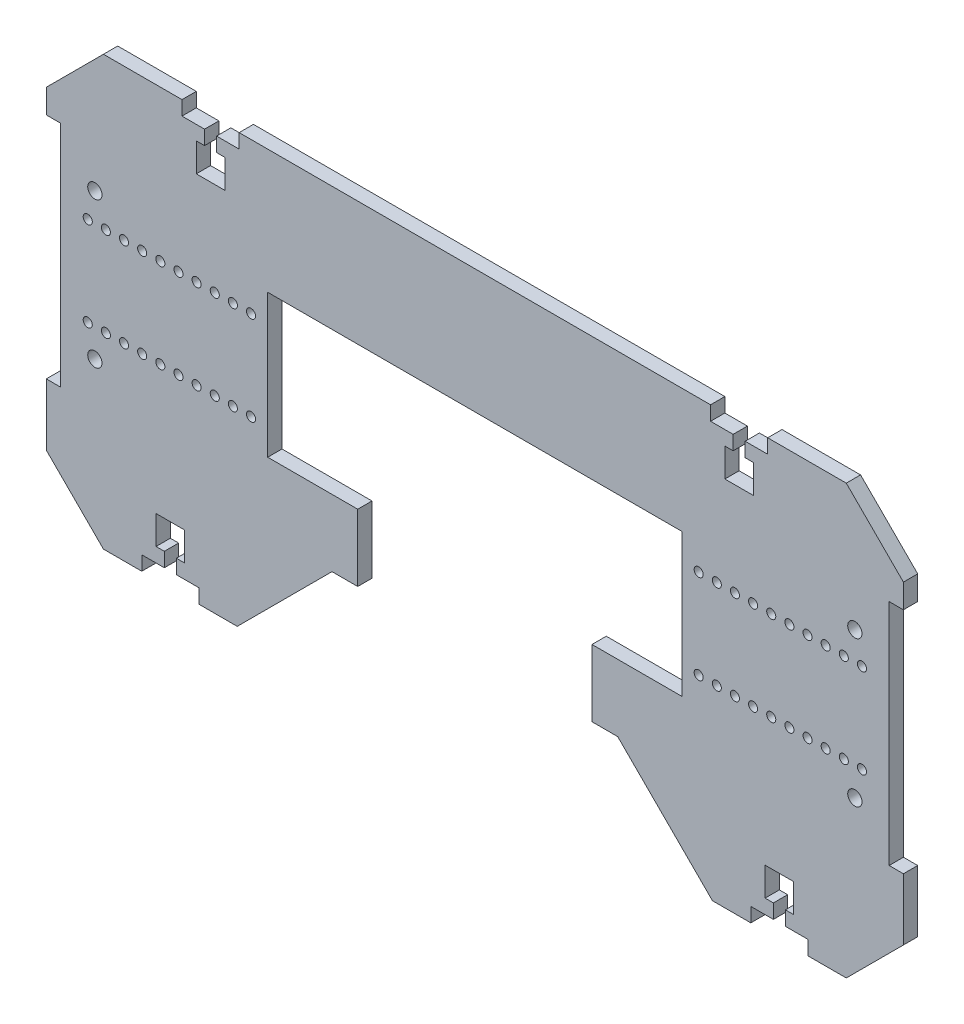
SolidWorks part; units mm, degrees
ref_plane "Front Plane" through (0, 0, 0) normal (0, 0, 1) x (1, 0, 0)
ref_plane "Top Plane" through (0, 0, 0) normal (0, 1, 0) x (1, 0, 0)
ref_plane "Right Plane" through (0, 0, 0) normal (1, 0, 0) x (0, 0, -1)
sketch "Sketch1" plane through (0, 0, 0) normal (0, 0, 1) x (1, 0, 0)
  line L3 (-32.7679, -18.8009) -> (-32.7679, 31.1991)
  line L4 (-72.7679, 31.1991) -> (-32.7679, 31.1991)
  line L5 (-32.7679, -18.8009) -> (-72.7679, -18.8009)
  line L6 (149.7321, -33.8009) -> (144.7321, -33.8009)
  line L7 (144.7321, -33.8009) -> (144.7321, 46.1991)
  line L8 (144.7321, 46.1991) -> (149.7321, 46.1991)
  line L9 (149.7321, 46.1991) -> (149.7321, 54.5982)
  line L10 (149.7321, 54.5982) -> (129.7321, 74.5982)
  line L11 (129.7321, 74.5982) -> (-130.2679, 74.5982)
  line L12 (-130.2679, 74.5982) -> (-150.2679, 54.5982)
  line L13 (-150.2679, 54.5982) -> (-150.2679, 46.1991)
  line L14 (-150.2679, 46.1991) -> (-145.2679, 46.1991)
  line L15 (-145.2679, 46.1991) -> (-145.2679, -33.8009)
  line L16 (-145.2679, -33.8009) -> (-150.2679, -33.8009)
  line L17 (-150.2679, -33.8009) -> (-150.2679, -55.4018)
  line L18 (-150.2679, -55.4018) -> (-130.2679, -75.4018)
  line L19 (-130.2679, -75.4018) -> (-83.4341, -75.4018)
  line L20 (-83.4341, -75.4018) -> (-50.2679, -42.2355)
  line L21 (-50.2679, -42.2355) -> (-28.2679, -42.2355)
  line L22 (49.7321, -42.2355) -> (82.8984, -75.4018)
  line L23 (82.8984, -75.4018) -> (129.7321, -75.4018)
  line L24 (129.7321, -75.4018) -> (149.7321, -55.4018)
  line L25 (149.7321, -55.4018) -> (149.7321, -33.8009)
  line L40 (27.7321, -42.2355) -> (49.7321, -42.2355)
  line L41 (-72.7679, 31.1991) -> (-72.7679, -18.8009)
  line L44 (-25.2679, -39.2355) -> (-25.2679, 1.2645)
  line L45 (-22.2679, 4.2645) -> (21.7321, 4.2645)
  line L46 (24.7321, -39.2355) -> (24.7321, 1.2645)
  line L47 (-32.7679, 31.1991) -> (-72.7679, -18.8009) construction
  line L48 (-52.7679, 6.1991) -> (-52.7679, 74.5982) construction
  line L49 (-52.7679, 6.1991) -> (-145.2679, 6.1991) construction
  line L50 (-0.2679, 74.5982) -> (-0.2679, 51.6893) construction
  line L51 (32.2321, -18.8009) -> (72.2321, -18.8009)
  line L52 (32.2321, -18.8009) -> (32.2321, 31.1991)
  line L53 (72.2321, 31.1991) -> (32.2321, 31.1991)
  line L54 (72.2321, 31.1991) -> (72.2321, -18.8009)
  arc A8 (24.7321, -39.2355) -> (27.7321, -42.2355) centre (27.7321, -39.2355) ccw
  arc A9 (-25.2679, -39.2355) -> (-28.2679, -42.2355) centre (-28.2679, -39.2355) cw
  arc A10 (21.7321, 4.2645) -> (24.7321, 1.2645) centre (21.7321, 1.2645) cw
  arc A11 (-25.2679, 1.2645) -> (-22.2679, 4.2645) centre (-22.2679, 1.2645) cw
  point P36 (24.7321, 4.2645)
  point P41 (-25.2679, 4.2645)
  point P56 (-0.2679, -20.7355)
  dimension "D22" = 3
  dimension "D1" = 260
  dimension "D2" = 28.2843
  dimension "D3" = 8.3991
  dimension "D4" = 80
  dimension "D5" = 21.6009
  dimension "D6" = 5
  dimension "D7" = 28.2843
  dimension "D8" = 46.8338
  dimension "D9" = 46.9042
  dimension "D10" = 46.9042
  dimension "D11" = 46.8338
  dimension "D12" = 28.2843
  dimension "D13" = 21.6009
  dimension "D14" = 80
  dimension "D15" = 8.3991
  dimension "D16" = 28.2843
  dimension "D17" = 40
  dimension "D18" = 50
  dimension "D21" = 50
extrude "Boss-Extrude1" add sketch "Sketch1" along normal blind 5
sketch "Sketch2" plane through (0, 0, 5) normal (0, 0, 1) x (1, 0, 0)
  line L0 (24.7321, 1.2645) -> (24.7321, -39.2355) construction
  line L1 (-25.2679, -39.2355) -> (-25.2679, 1.2645) construction
  line L2 (-22.2679, 4.2645) -> (21.7321, 4.2645) construction
  line L3 (24.7321, 1.2645) -> (24.7321, -39.2355)
  line L4 (-25.2679, -39.2355) -> (-25.2679, 1.2645)
  line L5 (-22.2679, 4.2645) -> (21.7321, 4.2645)
  line L6 (-29.2679, -38.3625) -> (-29.2679, 1.2645)
  line L7 (-22.2679, 8.2645) -> (21.7321, 8.2645)
  line L8 (28.7321, 1.2645) -> (28.7321, -38.3625)
  line L9 (-29.2679, -38.3625) -> (-29.2679, -42.2355)
  line L10 (-50.2679, -42.2355) -> (-28.2679, -42.2355) construction
  line L11 (28.7321, -38.3625) -> (28.7321, -42.2355)
  line L12 (27.7321, -42.2355) -> (49.7321, -42.2355) construction
  line L13 (27.7321, -42.2355) -> (28.7321, -42.2355)
  line L14 (-28.2679, -42.2355) -> (-29.2679, -42.2355)
  arc A0 (24.7321, -39.2355) -> (27.7321, -42.2355) centre (27.7321, -39.2355) ccw construction
  arc A1 (24.7321, 1.2645) -> (21.7321, 4.2645) centre (21.7321, 1.2645) ccw construction
  arc A2 (-28.2679, -42.2355) -> (-25.2679, -39.2355) centre (-28.2679, -39.2355) ccw construction
  arc A3 (-22.2679, 4.2645) -> (-25.2679, 1.2645) centre (-22.2679, 1.2645) ccw construction
  arc A4 (24.7321, -39.2355) -> (27.7321, -42.2355) centre (27.7321, -39.2355) ccw
  arc A5 (24.7321, 1.2645) -> (21.7321, 4.2645) centre (21.7321, 1.2645) ccw
  arc A6 (-28.2679, -42.2355) -> (-25.2679, -39.2355) centre (-28.2679, -39.2355) ccw
  arc A7 (-22.2679, 4.2645) -> (-25.2679, 1.2645) centre (-22.2679, 1.2645) ccw
  arc A8 (-29.2679, -38.3625) -> (-29.2679, -38.3625) centre (-29.2679, -38.3625) ccw
  arc A9 (-22.2679, 8.2645) -> (-29.2679, 1.2645) centre (-22.2679, 1.2645) ccw
  arc A10 (28.7321, 1.2645) -> (21.7321, 8.2645) centre (21.7321, 1.2645) ccw
  arc A11 (28.7321, -38.3625) -> (28.7321, -38.3625) centre (28.7321, -38.3625) ccw
  line M22 (-50.2679, -42.2355) -> (-28.2679, -42.2355)
  arc M23 (-28.2679, -42.2355) -> (-25.2679, -39.2355) centre (-28.2679, -39.2355) ccw
  line M24 (-25.2679, -39.2355) -> (-25.2679, 1.2645)
  arc M25 (-25.2679, 1.2645) -> (-22.2679, 4.2645) centre (-22.2679, 1.2645) cw
  line M26 (-22.2679, 4.2645) -> (21.7321, 4.2645)
  arc M27 (21.7321, 4.2645) -> (24.7321, 1.2645) centre (21.7321, 1.2645) cw
  line M28 (24.7321, 1.2645) -> (24.7321, -39.2355)
  arc M29 (24.7321, -39.2355) -> (27.7321, -42.2355) centre (27.7321, -39.2355) ccw
  line M30 (27.7321, -42.2355) -> (49.7321, -42.2355)
  dimension "D1" = 4
extrude "Cut-Extrude1" cut sketch "Sketch2" against normal through all contours L8 A10 L7 A9 L6 L9 L11 M22 M23 M24 M25 M26 M27 M28 M29 M30
fillet "Fillet1" radius 3 2 edges at (28.7321, -42.2355, 2.5) (-29.2679, -42.2355, 2.5)
sketch "Sketch3" plane through (0, 0, 5) normal (0, 0, 1) x (1, 0, 0)
  line L0 (-78.6054, -9.4219) -> (-84.9554, -9.4219) construction
  line L1 (-0.2679, 74.5982) -> (-0.2679, 39.9094) construction
  line L2 (129.7321, 74.5982) -> (-130.2679, 74.5982) construction
  line L3 (78.0696, -9.4219) -> (84.4196, -9.4219) construction
  circle A0 centre (-78.6054, -9.4219) radius 1.5875
  circle A1 centre (-78.6054, 21.8201) radius 1.5875
  circle A2 centre (-84.9554, -9.4219) radius 1.5875
  circle A3 centre (-84.9554, 21.8201) radius 1.5875
  circle A4 centre (-91.3054, -9.4219) radius 1.5875
  circle A5 centre (-91.3054, 21.8201) radius 1.5875
  circle A6 centre (-97.6554, -9.4219) radius 1.5875
  circle A7 centre (-97.6554, 21.8201) radius 1.5875
  circle A8 centre (-104.0054, -9.4219) radius 1.5875
  circle A9 centre (-104.0054, 21.8201) radius 1.5875
  circle A10 centre (-110.3554, -9.4219) radius 1.5875
  circle A11 centre (-110.3554, 21.8201) radius 1.5875
  circle A12 centre (-116.7054, -9.4219) radius 1.5875
  circle A13 centre (-116.7054, 21.8201) radius 1.5875
  circle A14 centre (-123.0554, -9.4219) radius 1.5875
  circle A15 centre (-123.0554, 21.8201) radius 1.5875
  circle A16 centre (-129.4054, -9.4219) radius 1.5875
  circle A17 centre (-129.4054, 21.8201) radius 1.5875
  circle A18 centre (-135.7554, -9.4219) radius 1.5875
  circle A19 centre (-135.7554, 21.8201) radius 1.5875
  circle A20 centre (135.2196, 21.8201) radius 1.5875
  circle A21 centre (135.2196, -9.4219) radius 1.5875
  circle A22 centre (128.8696, 21.8201) radius 1.5875
  circle A23 centre (128.8696, -9.4219) radius 1.5875
  circle A24 centre (122.5196, 21.8201) radius 1.5875
  circle A25 centre (122.5196, -9.4219) radius 1.5875
  circle A26 centre (116.1696, 21.8201) radius 1.5875
  circle A27 centre (116.1696, -9.4219) radius 1.5875
  circle A28 centre (109.8196, 21.8201) radius 1.5875
  circle A29 centre (109.8196, -9.4219) radius 1.5875
  circle A30 centre (103.4696, 21.8201) radius 1.5875
  circle A31 centre (103.4696, -9.4219) radius 1.5875
  circle A32 centre (97.1196, 21.8201) radius 1.5875
  circle A33 centre (97.1196, -9.4219) radius 1.5875
  circle A34 centre (90.7696, 21.8201) radius 1.5875
  circle A35 centre (90.7696, -9.4219) radius 1.5875
  circle A36 centre (84.4196, 21.8201) radius 1.5875
  circle A37 centre (84.4196, -9.4219) radius 1.5875
  circle A38 centre (78.0696, 21.8201) radius 1.5875
  circle A39 centre (78.0696, -9.4219) radius 1.5875
  dimension "D2" = 6.35
  dimension "D1" = 10
extrude "Cut-Extrude2" cut sketch "Sketch3" against normal through all
sketch "Sketch4" plane through (0, 0, 5) normal (0, 0, 1) x (1, 0, 0)
  line L0 (-41.2679, -42.2355) -> (-41.2679, -18.8009)
  line L1 (-50.2679, -42.2355) -> (-32.2679, -42.2355) construction
  line L2 (-72.7679, -18.8009) -> (-32.7679, -18.8009) construction
  line L3 (-22.2679, 8.2645) -> (-32.7679, 8.2645)
  line L4 (-32.7679, -18.8009) -> (-32.7679, 31.1991) construction
  line L5 (21.7321, 8.2645) -> (32.2321, 8.2645)
  line L6 (32.2321, 31.1991) -> (32.2321, -18.8009) construction
  line L7 (40.7321, -42.2355) -> (40.7321, -18.8009)
  line L8 (31.7321, -42.2355) -> (49.7321, -42.2355) construction
  line L9 (32.2321, -18.8009) -> (72.2321, -18.8009) construction
  line L10 (-29.2679, -39.2355) -> (-29.2679, 1.2645) construction
  line L11 (-29.2679, -39.2355) -> (-29.2679, 1.2645)
  line L12 (-41.2679, -42.2355) -> (-32.2679, -42.2355)
  line L13 (28.7321, 1.2645) -> (28.7321, -39.2355) construction
  line L14 (31.7321, -42.2355) -> (40.7321, -42.2355)
  line L15 (28.7321, 1.2645) -> (28.7321, -39.2355)
  line L17 (32.2321, 31.1991) -> (32.2321, -18.8009)
  line L18 (72.2321, 31.1991) -> (32.2321, 31.1991)
  line L19 (72.2321, -18.8009) -> (72.2321, 31.1991)
  line L20 (32.2321, -18.8009) -> (72.2321, -18.8009)
  line L21 (32.2321, 8.2645) -> (32.2321, -18.8009)
  line L24 (32.2321, -18.8009) -> (40.7321, -18.8009)
  line L25 (-72.7679, -18.8009) -> (-32.7679, -18.8009)
  line L26 (-72.7679, 31.1991) -> (-72.7679, -18.8009)
  line L27 (-32.7679, 31.1991) -> (-72.7679, 31.1991)
  line L28 (-32.7679, -18.8009) -> (-32.7679, 31.1991)
  line L29 (-41.2679, -18.8009) -> (-32.7679, -18.8009)
  line L32 (-32.7679, -18.8009) -> (-32.7679, 8.2645)
  arc A0 (-32.2679, -42.2355) -> (-29.2679, -39.2355) centre (-32.2679, -39.2355) ccw construction
  arc A1 (-32.2679, -42.2355) -> (-29.2679, -39.2355) centre (-32.2679, -39.2355) ccw
  arc A2 (28.7321, -39.2355) -> (31.7321, -42.2355) centre (31.7321, -39.2355) ccw construction
  arc A3 (28.7321, 1.2645) -> (21.7321, 8.2645) centre (21.7321, 1.2645) ccw construction
  arc A4 (-22.2679, 8.2645) -> (-29.2679, 1.2645) centre (-22.2679, 1.2645) ccw construction
  arc A5 (28.7321, -39.2355) -> (31.7321, -42.2355) centre (31.7321, -39.2355) ccw
  arc A6 (28.7321, 1.2645) -> (21.7321, 8.2645) centre (21.7321, 1.2645) ccw
  arc A7 (-22.2679, 8.2645) -> (-29.2679, 1.2645) centre (-22.2679, 1.2645) ccw
  dimension "D1" = 0
  dimension "D2" = 0
extrude "Cut-Extrude3" cut sketch "Sketch4" against normal through all
sketch "Sketch6" plane through (0, 0, 5) normal (0, 0, 1) x (1, 0, 0)
  line L0 (-92.7679, 77.0982) -> (-92.7679, 60.9572) construction
  line L1 (-0.2679, 77.0982) -> (-0.2679, 60.9572) construction
  line L2 (-106.851, -77.9018) -> (-106.851, -66.1434) construction
  line L3 (-102.7679, 74.5982) -> (-102.7679, 69.5982) construction
  line L4 (-82.7679, 74.5982) -> (-82.7679, 69.5982) construction
  line L5 (-102.7679, 74.5982) -> (-102.7679, 69.5982)
  line L6 (-82.7679, 74.5982) -> (-82.7679, 69.5982)
  line L7 (-102.7679, 69.5982) -> (-94.8679, 69.5982)
  line L8 (-94.8679, 69.5982) -> (-94.8679, 64.5982)
  line L9 (-94.8679, 64.5982) -> (-97.7679, 64.5982)
  line L10 (-97.7679, 64.5982) -> (-97.7679, 54.5982)
  line L11 (-97.7679, 54.5982) -> (-87.7679, 54.5982)
  line L12 (-87.7679, 54.5982) -> (-87.7679, 64.5982)
  line L13 (-87.7679, 64.5982) -> (-90.6679, 64.5982)
  line L14 (-90.6679, 64.5982) -> (-90.6679, 69.5982)
  line L15 (-102.7679, 74.5982) -> (-82.7679, 74.5982)
  line L16 (-90.6679, 69.5982) -> (-82.7679, 69.5982)
  line L17 (-116.851, -75.4018) -> (-116.851, -70.4018) construction
  line L18 (-96.851, -70.4018) -> (-96.851, -75.4018) construction
  line L19 (-116.851, -75.4018) -> (-116.851, -70.4018)
  line L20 (-96.851, -70.4018) -> (-96.851, -75.4018)
  line L21 (-116.851, -75.4018) -> (-96.851, -75.4018)
  line L22 (-116.851, -70.4018) -> (-108.951, -70.4018)
  line L23 (-108.951, -70.4018) -> (-108.951, -65.4018)
  line L24 (-108.951, -65.4018) -> (-111.851, -65.4018)
  line L25 (-111.851, -65.4018) -> (-111.851, -55.4018)
  line L26 (-111.851, -55.4018) -> (-101.851, -55.4018)
  line L27 (-101.851, -55.4018) -> (-101.851, -65.4018)
  line L28 (-101.851, -65.4018) -> (-104.751, -65.4018)
  line L29 (-104.751, -65.4018) -> (-104.751, -70.4018)
  line L30 (-104.751, -70.4018) -> (-96.851, -70.4018)
  line L31 (106.3153, -77.9018) -> (106.3153, -66.1434) construction
  line L32 (92.2321, 77.0982) -> (92.2321, 60.9572) construction
  line L33 (104.2153, -70.4018) -> (96.3153, -70.4018)
  line L34 (104.2153, -65.4018) -> (104.2153, -70.4018)
  line L35 (101.3153, -65.4018) -> (104.2153, -65.4018)
  line L36 (101.3153, -55.4018) -> (101.3153, -65.4018)
  line L37 (111.3153, -55.4018) -> (101.3153, -55.4018)
  line L38 (111.3153, -65.4018) -> (111.3153, -55.4018)
  line L39 (108.4153, -65.4018) -> (111.3153, -65.4018)
  line L40 (108.4153, -70.4018) -> (108.4153, -65.4018)
  line L41 (116.3153, -70.4018) -> (108.4153, -70.4018)
  line L42 (116.3153, -75.4018) -> (96.3153, -75.4018)
  line L43 (96.3153, -70.4018) -> (96.3153, -75.4018)
  line L44 (116.3153, -75.4018) -> (116.3153, -70.4018)
  line L45 (90.1321, 69.5982) -> (82.2321, 69.5982)
  line L46 (102.2321, 74.5982) -> (82.2321, 74.5982)
  line L47 (90.1321, 64.5982) -> (90.1321, 69.5982)
  line L48 (87.2321, 64.5982) -> (90.1321, 64.5982)
  line L49 (87.2321, 54.5982) -> (87.2321, 64.5982)
  line L50 (97.2321, 54.5982) -> (87.2321, 54.5982)
  line L51 (97.2321, 64.5982) -> (97.2321, 54.5982)
  line L52 (94.3321, 64.5982) -> (97.2321, 64.5982)
  line L53 (94.3321, 69.5982) -> (94.3321, 64.5982)
  line L54 (102.2321, 69.5982) -> (94.3321, 69.5982)
  line L55 (82.2321, 74.5982) -> (82.2321, 69.5982)
  line L56 (102.2321, 74.5982) -> (102.2321, 69.5982)
  arc A0 (-88.4377, 74.5982) -> (-97.098, 74.5982) centre (-92.7679, 72.0982) ccw construction
  arc A1 (4.0623, 74.5982) -> (-4.598, 74.5982) centre (-0.2679, 72.0982) ccw construction
  arc A2 (-111.1811, -75.4018) -> (-102.5208, -75.4018) centre (-106.851, -72.9018) ccw construction
  dimension "D1" = 2.1
  dimension "D2" = 4.2
  dimension "D3" = 5
  dimension "D4" = 10
  dimension "D5" = 5
  dimension "D6" = 10
  dimension "D7" = 2.1
  dimension "D8" = 4.2
  dimension "D9" = 5
  dimension "D10" = 5
  dimension "D11" = 10
  dimension "D12" = 10
  dimension "D13" = 5
extrude "Cut-Extrude5" cut sketch "Sketch6" against normal blind 5
sketch "Sketch7" plane through (0, 0, 5) normal (0, 0, 1) x (1, 0, 0)
  circle A0 centre (-133.2679, -19.3009) radius 2.5 construction
  circle A1 centre (-133.2679, 31.6991) radius 2.5 construction
  circle A2 centre (-133.2679, -19.3009) radius 2.5
  circle A3 centre (-133.2679, 31.6991) radius 2.5
  circle A4 centre (132.7321, -19.3009) radius 2.5 construction
  circle A5 centre (132.7321, 31.6991) radius 2.5 construction
  circle A6 centre (132.7321, -19.3009) radius 2.5
  circle A7 centre (132.7321, 31.6991) radius 2.5
extrude "Cut-Extrude6" cut sketch "Sketch7" against normal blind 5
sketch "Sketch8" plane through (0, 0, 5) normal (0, 0, 1) x (1, 0, 0)
  line L0 (32.2321, 31.1991) -> (32.2321, 8.2645) construction
  line L1 (-32.7679, 8.2645) -> (-32.7679, 31.1991) construction
  line L2 (-32.7679, 8.2645) -> (32.2321, 8.2645) construction
  line L3 (32.2321, 31.1991) -> (32.2321, 8.2645)
  line L4 (-32.7679, 8.2645) -> (-32.7679, 31.1991)
  line L5 (-32.7679, 8.2645) -> (32.2321, 8.2645)
  line L6 (-32.7679, 31.1991) -> (32.2321, 31.1991)
extrude "Cut-Extrude7" cut sketch "Sketch8" against normal blind 5
